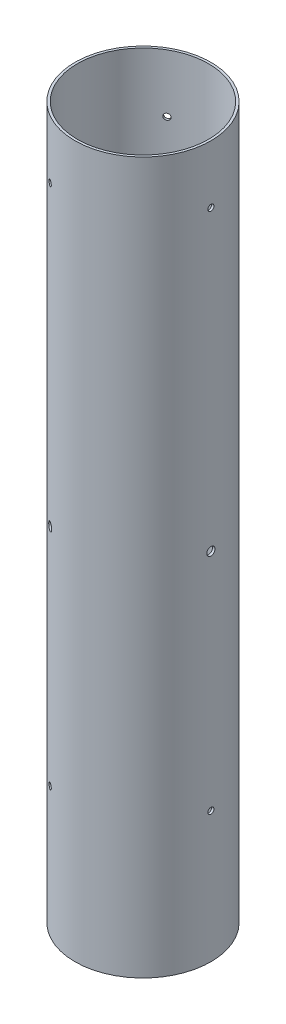
SolidWorks part; units mm, degrees
material "G12 Fiberglass"
ref_plane "Front Plane" through (0, 0, 0) normal (0, 0, 1) x (1, 0, 0)
ref_plane "Top Plane" through (0, 0, 0) normal (0, 1, 0) x (1, 0, 0)
ref_plane "Right Plane" through (0, 0, 0) normal (1, 0, 0) x (0, 0, -1)
sketch "Sketch1" plane through (0, 0, 0) normal (0, 1, 0) x (1, 0, 0)
  circle A0 centre (0, 0) radius 38.227
  circle A1 centre (0, 0) radius 39.624
  dimension "D1" = 76.454
  dimension "D2" = 79.248
extrude "Boss-Extrude1" add sketch "Sketch1" along normal blind 414.3375
ref_axis "Axis1" through (0, -7.62, 0) along (0, 1, 0)
ref_plane "Plane1" through (-19.812, 0, 34.3154) normal (-0.5, 0, 0.866) x (0, -1, 0)
sketch "Sketch2" plane through (-19.812, 0, 34.3154) normal (-0.5, 0, 0.866) x (0, -1, 0)
  line L0 (7.62, 0) -> (-160.02, 0) construction
  line L2 (0, -39.624) -> (0, 39.624) construction
  circle A0 centre (-76.2, 0) radius 1.778
  dimension "D1" = 76.2
  dimension "D2" = 3.556
extrude "Cut-Extrude1" cut sketch "Sketch2" against normal up to next
pattern_circular "CirPattern1" count 3 over 360 about axis through (0, -7.62, 0) along (0, 1, 0) of "Cut-Extrude1"
ref_plane "Plane2" through (0, 207.1687, 0) normal (0, 1, 0) x (1, 0, 0)
sketch "Sketch3" plane through (-19.812, 0, 34.3154) normal (-0.5, 0, 0.866) x (0, -1, 0)
  line L0 (-207.1687, 43.6423) -> (-207.1687, -43.6423) construction
  circle A0 centre (-207.1687, 0) radius 2.3813
  dimension "D1" = 4.7625
extrude "Pressure Equalization Hole" cut sketch "Sketch3" against normal up to next
pattern_circular "CirPattern2" count 3 over 360 about axis through (0, -7.62, 0) along (0, 1, 0) of "Pressure Equalization Hole"
ref_plane "Plane3" through (39.624, 0, 0) normal (1, 0, 0) x (0, 0, -1)
sketch "Sketch4" plane through (39.624, 0, 0) normal (-1, 0, 0) x (0, -1, 0)
  line L0 (-414.3375, 39.624) -> (-414.3375, -39.624) construction
  circle A0 centre (-380.5301, 0) radius 1.7859
  dimension "D1" = 3.5719
  dimension "D2" = 33.8074
extrude "Cut-Extrude3" cut sketch "Sketch4" along normal up to next
pattern_circular "CirPattern3" count 3 over 360 about axis through (0, -7.62, 0) along (0, 1, 0) of "Cut-Extrude3"
